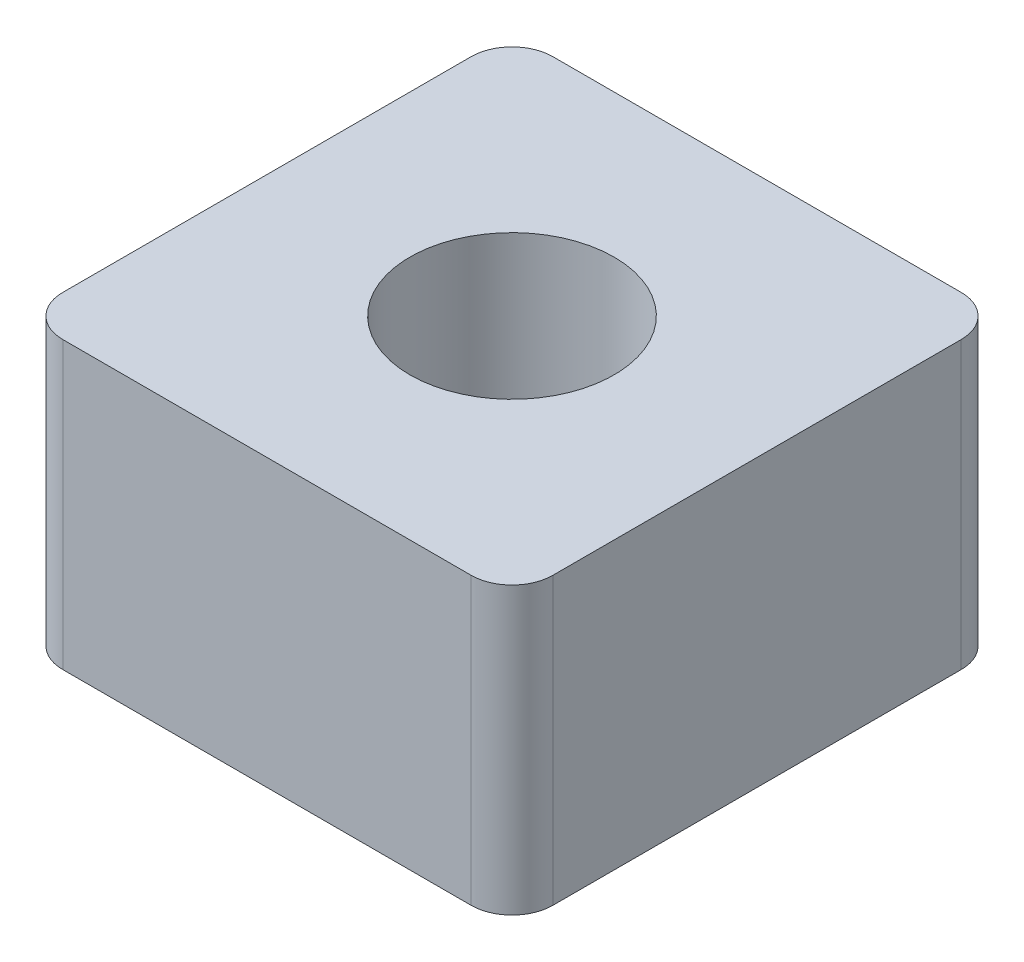
SolidWorks part; units mm, degrees
ref_plane "Front Plane" through (0, 0, 0) normal (0, 0, 1) x (1, 0, 0)
ref_plane "Top Plane" through (0, 0, 0) normal (0, 1, 0) x (1, 0, 0)
ref_plane "Right Plane" through (0, 0, 0) normal (1, 0, 0) x (0, 0, -1)
other "Configuration Table"
sketch "Sketch2" plane through (0, 0, 0) normal (0, 1, 0) x (1, 0, 0)
  line L1 (-50, -60) -> (50, -60)
  line L2 (-60, -50) -> (-60, 50)
  line L3 (-50, 60) -> (50, 60)
  line L4 (60, -50) -> (60, 50)
  line L5 (-60, -60) -> (60, 60) construction
  line L6 (-60, 60) -> (60, -60) construction
  arc A0 (50, -60) -> (60, -50) centre (50, -50) ccw
  arc A1 (-50, -60) -> (-60, -50) centre (-50, -50) cw
  arc A2 (60, 50) -> (50, 60) centre (50, 50) ccw
  arc A3 (-60, 50) -> (-50, 60) centre (-50, 50) cw
  point P1 (0, 0)
  dimension "D3" = 10
  dimension "D1" = 120
  dimension "D2" = 120
extrude "Boss-Extrude1" add sketch "Sketch2" along normal blind 70 contours L3 A2 L4 A0 L1 A1 L2 A3
sketch "Sketch4" plane through (0, 0, 0) normal (0, -1, 0) x (1, 0, 0)
  circle A0 centre (0, 0) radius 35
  circle A1 centre (0, 0) radius 25
extrude "Cut-Extrude4" cut sketch "Sketch4" against normal through all contours A1
